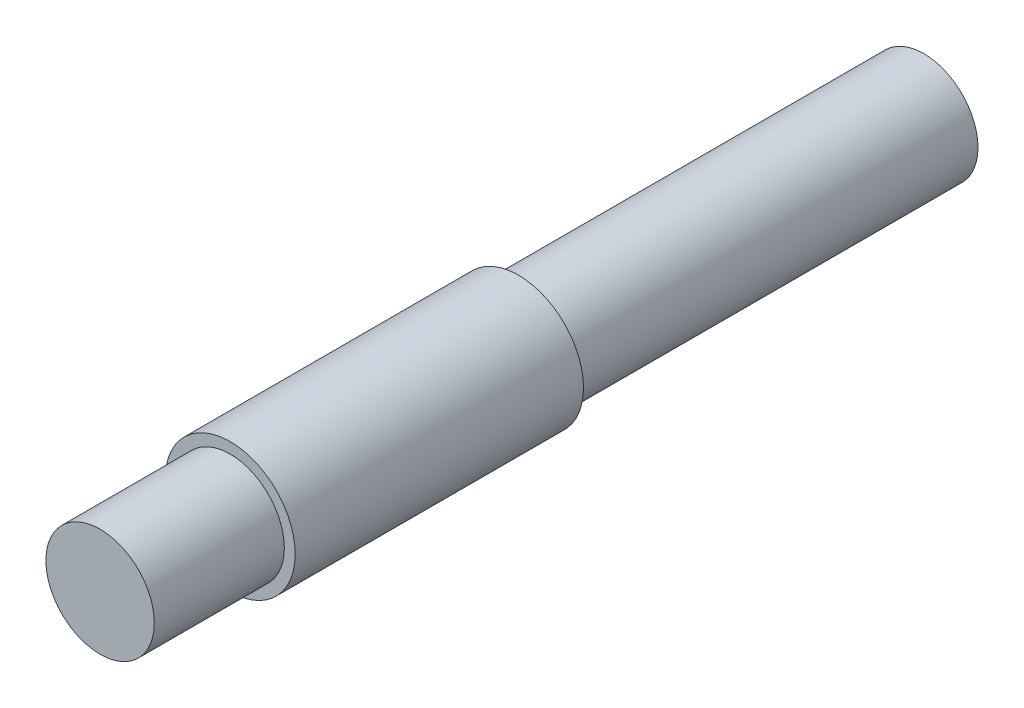
SolidWorks part; units mm, degrees
ref_plane "正面" through (0, 0, 0) normal (0, 0, 1) x (1, 0, 0)
ref_plane "平面" through (0, 0, 0) normal (0, 1, 0) x (1, 0, 0)
ref_plane "右側面" through (0, 0, 0) normal (1, 0, 0) x (0, 0, -1)
sketch "ｽｹｯﾁ1" plane through (0, 0, 0) normal (0, 0, 1) x (1, 0, 0)
  circle A0 centre (0, 0) radius 2.5
  dimension "D1" = 5
extrude "ﾎﾞｽ - 押し出し1" add sketch "ｽｹｯﾁ1" along normal blind 18.7
sketch "ｽｹｯﾁ2" plane through (0, 0, 18.7) normal (0, 0, 1) x (1, 0, 0)
  circle A0 centre (0, 0) radius 3
  dimension "D1" = 6
extrude "ﾎﾞｽ - 押し出し2" add sketch "ｽｹｯﾁ2" along normal blind 13.3
sketch "ｽｹｯﾁ3" plane through (0, 0, 32) normal (0, 0, 1) x (1, 0, 0)
  circle A0 centre (0, 0) radius 2.5
  dimension "D1" = 5
extrude "ﾎﾞｽ - 押し出し3" add sketch "ｽｹｯﾁ3" along normal blind 6 contours A0
